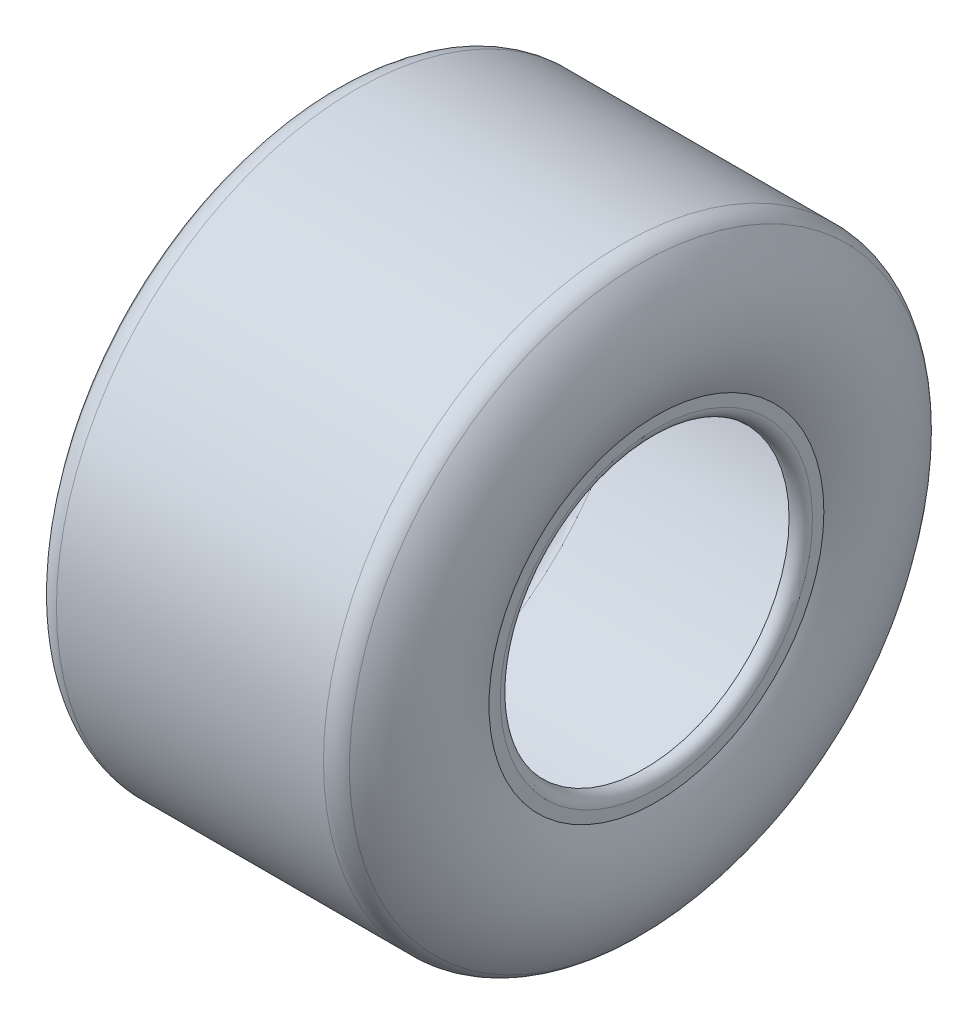
SolidWorks part; units mm, degrees
ref_plane "Front Plane" through (0, 0, 0) normal (0, 0, 1) x (1, 0, 0)
ref_plane "Top Plane" through (0, 0, 0) normal (0, 1, 0) x (1, 0, 0)
ref_plane "Right Plane" through (0, 0, 0) normal (1, 0, 0) x (0, 0, -1)
sketch "Sketch1" plane through (0, 0, 0) normal (0, 0, 1) x (1, 0, 0)
  line L0 (0, 0) -> (0, 125) construction
  line L1 (0, 0) -> (-113.19, 0) construction
  line L2 (-70, 70) -> (-70, 65.23)
  line L3 (0, 125) -> (-55.8152, 125)
  line L4 (0, 120) -> (-55.8152, 120)
  line L5 (-65, 71.223) -> (-65, 60.46)
  line L6 (-70, 70) -> (-70, 60.46) construction
  line L7 (65, 71.223) -> (65, 60.46)
  line L8 (0, 120) -> (55.8152, 120)
  line L9 (0, 125) -> (55.8152, 125)
  line L10 (70, 70) -> (70, 65.23)
  arc A0 (-63.3059, 121.6249) -> (-70, 70) centre (-28.531, 90.8693) ccw
  arc A1 (-55.8152, 125) -> (-63.3059, 121.6249) centre (-55.8152, 115) ccw
  arc A2 (-55.8152, 120) -> (-59.5606, 118.3125) centre (-55.8152, 115) ccw
  arc A3 (-59.5606, 118.3125) -> (-65, 71.223) centre (-28.531, 90.8693) ccw
  arc A4 (-65, 60.46) -> (-70, 65.23) centre (-65.115, 65.345) cw
  arc A5 (65, 60.46) -> (70, 65.23) centre (65.115, 65.345) ccw
  arc A6 (59.5606, 118.3125) -> (65, 71.223) centre (28.531, 90.8693) cw
  arc A7 (55.8152, 120) -> (59.5606, 118.3125) centre (55.8152, 115) cw
  arc A8 (55.8152, 125) -> (63.3059, 121.6249) centre (55.8152, 115) cw
  arc A9 (63.3059, 121.6249) -> (70, 70) centre (28.531, 90.8693) cw
  point P1 (60, 125)
  point P12 (-60, 125)
  dimension "D7" = 10
  dimension "D1" = 60
  dimension "D2" = 125
  dimension "D5" = 70
  dimension "D6" = 5
revolve "Revolve1" add sketch "Sketch1" angle 360 about L1
